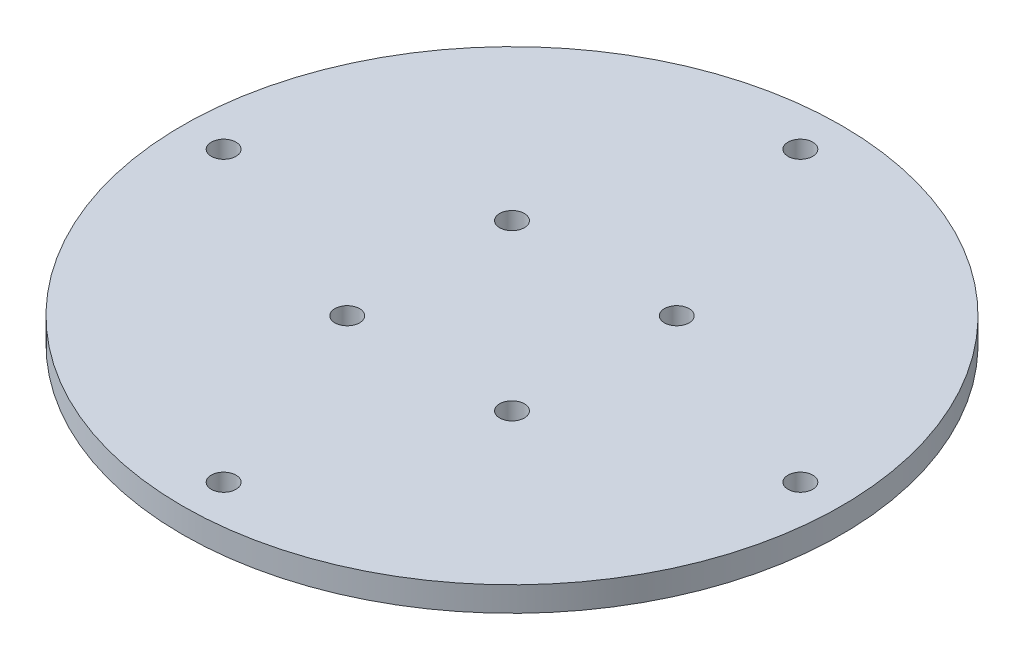
SolidWorks part; units mm, degrees
ref_plane "Front Plane" through (0, 0, 0) normal (0, 0, 1) x (1, 0, 0)
ref_plane "Top Plane" through (0, 0, 0) normal (0, 1, 0) x (1, 0, 0)
ref_plane "Right Plane" through (0, 0, 0) normal (1, 0, 0) x (0, 0, -1)
sketch "Sketch1" plane through (0, 0, 0) normal (0, 1, 0) x (1, 0, 0)
  line L0 (0, 40) -> (0, -40) construction
  line L1 (-40, 0) -> (40, 0) construction
  circle A0 centre (0, 0) radius 40
  circle A1 centre (0, 35) radius 1.5
  circle A2 centre (35, 0) radius 1.5
  circle A3 centre (0, -35) radius 1.5
  circle A4 centre (-35, 0) radius 1.5
  dimension "D1" = 80
  dimension "D2" = 3
  dimension "D3" = 3
  dimension "D4" = 3
  dimension "D5" = 3
  dimension "D6" = 5
  dimension "D7" = 5
  dimension "D8" = 5
  dimension "D9" = 5
extrude "Boss-Extrude1" add sketch "Sketch1" along normal blind 3
sketch "Sketch2" plane through (0, 3, 0) normal (0, 1, 0) x (1, 0, 0)
  line L0 (-10, 10) -> (10, -10) construction
  line L1 (-10, 10) -> (10, 10) construction
  line L2 (-10, 10) -> (-10, -10) construction
  line L3 (-10, -10) -> (10, -10) construction
  line L4 (10, 10) -> (10, -10) construction
  circle A0 centre (10, 10) radius 1.5
  circle A1 centre (-10, 10) radius 1.5
  circle A2 centre (-10, -10) radius 1.5
  circle A3 centre (10, -10) radius 1.5
  point P4 (0, 0)
  dimension "D3" = 3
  dimension "D4" = 3
  dimension "D5" = 3
  dimension "D6" = 3
  dimension "D1" = 20
  dimension "D2" = 20
extrude "Cut-Extrude1" cut sketch "Sketch2" against normal blind 3
